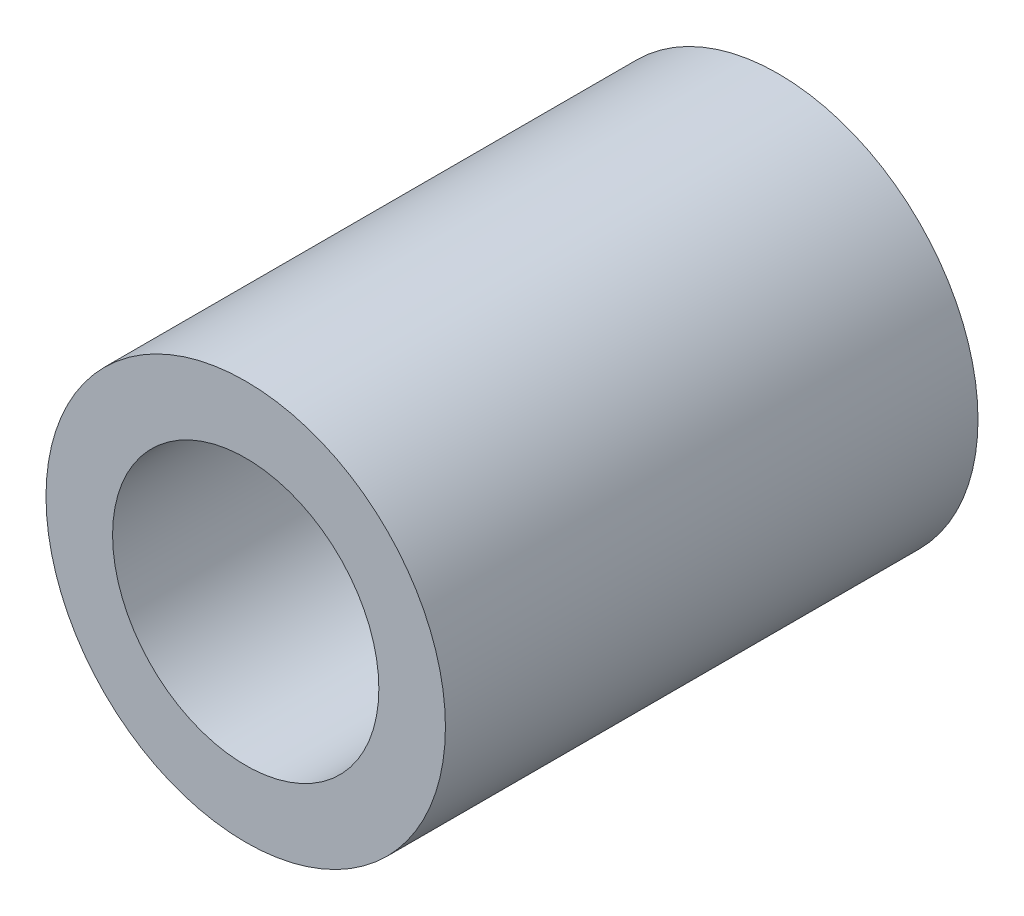
SolidWorks part; units mm, degrees
material "Brass"
ref_plane "Front Plane" through (0, 0, 0) normal (0, 0, 1) x (1, 0, 0)
ref_plane "Top Plane" through (0, 0, 0) normal (0, 1, 0) x (1, 0, 0)
ref_plane "Right Plane" through (0, 0, 0) normal (1, 0, 0) x (0, 0, -1)
sketch "Sketch1" plane through (0, 0, 0) normal (0, 0, 1) x (1, 0, 0)
  circle A0 centre (0, 0) radius 4.7625
  circle A1 centre (0, 0) radius 3.175
  dimension "D1" = 6.35
  dimension "D2" = 9.525
extrude "Boss-Extrude1" add sketch "Sketch1" along normal blind 12.7
